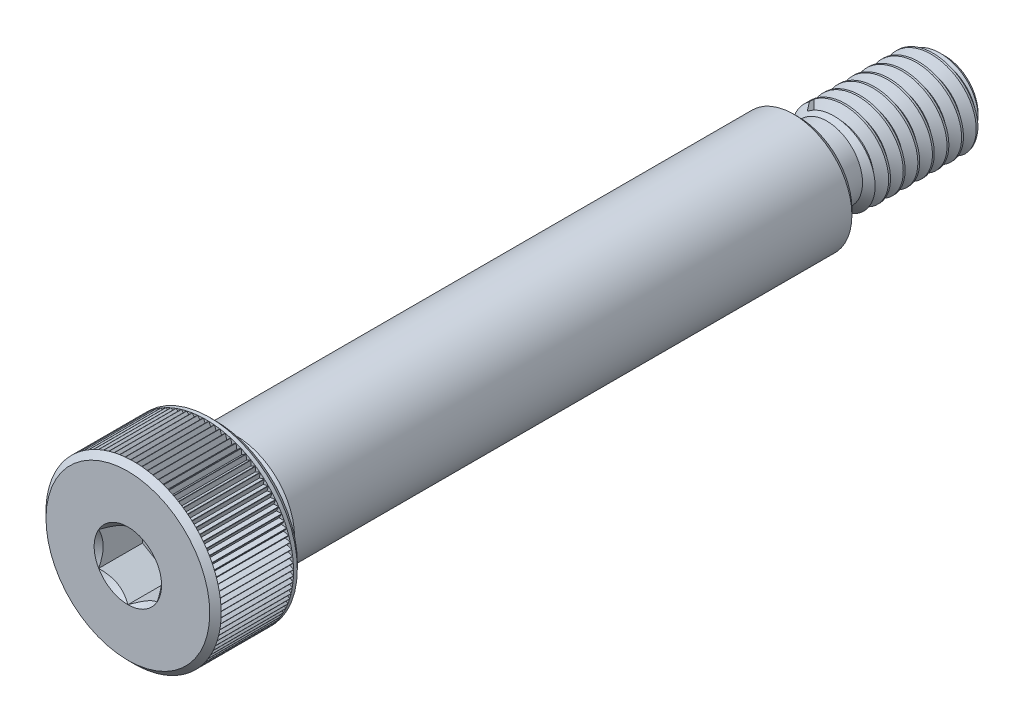
SolidWorks part; units mm, degrees
material "Stainless Steel (ferritic)"
ref_plane "Front Plane" through (0, 0, 0) normal (0, 0, 1) x (1, 0, 0)
ref_plane "Top Plane" through (0, 0, 0) normal (0, 1, 0) x (1, 0, 0)
ref_plane "Right Plane" through (0, 0, 0) normal (1, 0, 0) x (0, 0, -1)
sketch "Sketch1" plane through (0, 0, 0) normal (1, 0, 0) x (0, 0, -1)
  line L0 (-14, 0) -> (14, 0) construction
  line L1 (-14, -3) -> (-14, 3) construction
  line L2 (-14, 3) -> (-11, 3) construction
  line L3 (-11, 3) -> (-11, 1.797) construction
  line L4 (-11, 1.797) -> (-10.492, 1.797) construction
  line L5 (-10.492, 1.797) -> (-10.289, 2) construction
  line L6 (-10.289, 2) -> (9, 2) construction
  line L7 (13.9688, 1.5541) -> (14.2188, 1.1211) construction
  line L8 (14.2188, 1.1211) -> (14.4688, 1.5541) construction
  line L9 (14, -1.5) -> (14, 1.5) construction
  line L10 (9, 2) -> (14, 2) construction
  line L11 (14.4688, 1.5541) -> (13.9688, 1.5541) construction
  line L12 (14.2188, 1.5541) -> (14.2188, 1.5) construction
  line L13 (14.2188, 1.1211) -> (14.2188, 1.1752) construction
  line L14 (14.25, 1.1752) -> (14.1875, 1.1752) construction
  line L15 (14.4375, 1.5) -> (14, 1.5) construction
  line L16 (14.2188, 1.5271) -> (14.4531, 1.5271) construction
  line L17 (14.2188, 1.5271) -> (13.9844, 1.5271) construction
  line L18 (-14, 2.805) -> (-13.805, 3) construction
  line L19 (-11.195, 3) -> (-11, 2.805) construction
  line L20 (14, 1.5) -> (9, 1.5) construction
  line L21 (13.625, 1.5) -> (14, 1.125) construction
  line L22 (10.2313, 1.5) -> (9.95, 1.2187) construction
  line L23 (9.95, 1.2187) -> (9.1406, 1.2187) construction
  line L24 (9, 1.5) -> (9, 1.3594) construction
  line L25 (-12.5, 1) -> (-12.5, -1) construction
  line L26 (-12.5, -1) -> (-14, -1) construction
  line L27 (-12.5, 1) -> (-14, 1) construction
  line L28 (-13.805, 0) -> (-11.3255, 0) construction
  arc A0 (9, 1.3594) -> (9.1406, 1.2187) centre (9.1406, 1.3594) ccw construction
  point P4 (0, 0)
  point P7 (-14, 0)
  point P18 (14, 0)
  point P25 (12.25, -1.5)
  point P38 (-12.5, 3)
  point P45 (-12.5, 0)
  point P46 (10.0906, 1.3594)
  point P48 (-10.492, 0)
  point P51 (-12.5, 0)
  point P52 (9, 0)
  point P53 (-9.2, 0)
  dimension "Head Diameter" = 6
  dimension "Head Height" = 3
  dimension "Thread Diameter" = 3
  dimension "Shoulder Diameter" = 4
  dimension "Thread Length" = 5
  dimension "D1" = 0.508
  dimension "D2" = 135
  dimension "D3" = 0.203
  dimension "Shoulder Length" = 20
  dimension "Thread Pitch" = 0.5
  dimension "D4" = 0.0625
  dimension "D5" = 1.75
  dimension "D6" = 0.195
  dimension "D7" = 0.375
  dimension "D8" = 2.4375
  dimension "D9" = 0.95
  dimension "Drive Size" = 2
  dimension "Knurling Length" = 2.4795
  dimension "D10" = 4.8
sketch "Sketch3" plane through (0, 0, 0) normal (1, 0, 0) x (0, 0, -1)
  line L0 (-14, 0) -> (-14, 2.805)
  line L1 (-14, -3) -> (-14, 3) construction
  line L2 (-14, 2.805) -> (-13.805, 3)
  line L3 (-13.805, 3) -> (-11.195, 3)
  line L4 (-11.195, 3) -> (-11, 2.805)
  line L5 (-11, 2.805) -> (-11, 1.797)
  line L6 (-11, 1.797) -> (-10.492, 1.797)
  line L7 (-10.492, 1.797) -> (-10.289, 2)
  line L8 (-10.289, 2) -> (9, 2)
  line L9 (9, 2) -> (9, 1.3594)
  line L10 (9.1406, 1.2187) -> (9.95, 1.2187)
  line L11 (9.95, 1.2187) -> (10.2313, 1.5)
  line L12 (10.2313, 1.5) -> (13.625, 1.5)
  line L13 (13.625, 1.5) -> (14, 1.125)
  line L14 (14, 1.125) -> (14, 0)
  line L15 (14, 0) -> (-14, 0)
  arc A0 (9, 1.3594) -> (9.1406, 1.2187) centre (9.1406, 1.3594) ccw construction
  arc A1 (9, 1.3594) -> (9.1406, 1.2187) centre (9.1406, 1.3594) ccw
revolve "Revolve1" add sketch "Sketch3" angle 360 about L0
sketch "Sketch4" plane through (0, 0, 0) normal (0, 0, 1) x (1, 0, 0)
  line L0 (0, -3) -> (0, 3) construction
  line L1 (0, 1.1547) -> (-1, 0.5774)
  line L2 (-1, 0.5774) -> (-1, -0.5774)
  line L3 (-1, -0.5774) -> (0, -1.1547)
  line L4 (0, -1.1547) -> (1, -0.5774)
  line L5 (1, -0.5774) -> (1, 0.5774)
  line L6 (1, 0.5774) -> (0, 1.1547)
  circle A0 centre (0, 0) radius 1 construction
extrude "Cut-Extrude1" cut sketch "Sketch4" against normal up to vertex (-12.5 mm away) from vertex at 14 starting at point (0, 0, 14)
sketch "Sketch5" plane through (0, 0, 0) normal (0, 0, 1) x (1, 0, 0)
  line L0 (0, -3) -> (0, 3) construction
  circle A0 centre (0, 0) radius 1.1547
extrude "Cut-Extrude2" cut sketch "Sketch5" against normal up to vertex (-12.5 mm away) draft 45 from vertex at 14 starting at point (0, 0, 14)
chamfer "Chamfer1" distance 0.195 angle 45 1 edges at (2, 0, -9)
sketch "Sketch6" plane through (0, 0, -14) normal (0, 0, -1) x (-1, 0, 0)
  circle A0 centre (0, 0) radius 1.5
curve "Helix/Spiral1" pitch 0.5 height 4.05 turns 8.1
sketch "Sketch7" plane through (0, 0, 0) normal (1, 0, 0) x (0, 0, -1)
  line L0 (13.9844, 1.5271) -> (14.1875, 1.1752)
  line L1 (14.1875, 1.1752) -> (14.25, 1.1752)
  line L2 (14.25, 1.1752) -> (14.4531, 1.5271)
  line L3 (14.4531, 1.5271) -> (13.9844, 1.5271)
sweep "Cut-Sweep1" cut profiles "Sketch7" path "Helix/Spiral1"
sketch "Sketch8" plane through (0, 0, 0) normal (0, 0, 1) x (1, 0, 0)
  line L0 (0, 3) -> (0, 0) construction
  line L1 (-0.0901, 3) -> (0.0901, 3)
  line L2 (0.0901, 3) -> (0, 2.844)
  line L3 (0, 2.844) -> (-0.0901, 3)
  line L4 (-0.0901, 3) -> (0, 0) construction
  line L5 (0, 0) -> (0.0901, 3) construction
  circle A0 centre (0, 0) radius 2.844 construction
  point P8 (0, 3)
  dimension "D1" = 0.156
  dimension "D2" = 3.439
extrude "Cut-Extrude3" cut sketch "Sketch8" against normal up to vertex (-11.3255 mm away) from vertex at 13.805 starting at point (0, 0, 13.805)
pattern_circular "CirPattern1" count 99 over 360 about axis through (0, 0, 0) along (0, 0, 1) of "Cut-Extrude3"
equation "\"D4@Sketch1\"=\"Thread Pitch@Sketch1\"/8"
equation "\"D5@Sketch1\"=\"Thread Pitch@Sketch1\"*3.5"
equation "\"D6@Sketch1\"=\"Head Diameter@Sketch1\"*.0325"
equation "\"D7@Sketch1\"=\"Thread Pitch@Sketch1\"*.75"
equation "\"D1@Chamfer1\"=\"D6@Sketch1\""
equation "\"D4@Helix/Spiral1\"=\"Thread Pitch@Sketch1\""
equation "\"D3@Helix/Spiral1\" = \"Thread Length@Sketch1\" - \"D9@Sketch1\""
equation "\"D1@Sketch8\"=\"D6@Sketch1\"*.8"
equation "\"D1@CirPattern1\"=(360/\"D2@Sketch8\")-6"
equation "\"D9@Sketch1\"  = \"Thread Length@Sketch1\"*.2"
equation "\"D8@Sketch1\"=\"Thread Diameter@Sketch1\"*.65"
equation "\"D10@Sketch1\"=\"Head Diameter@Sketch1\"*.8"
